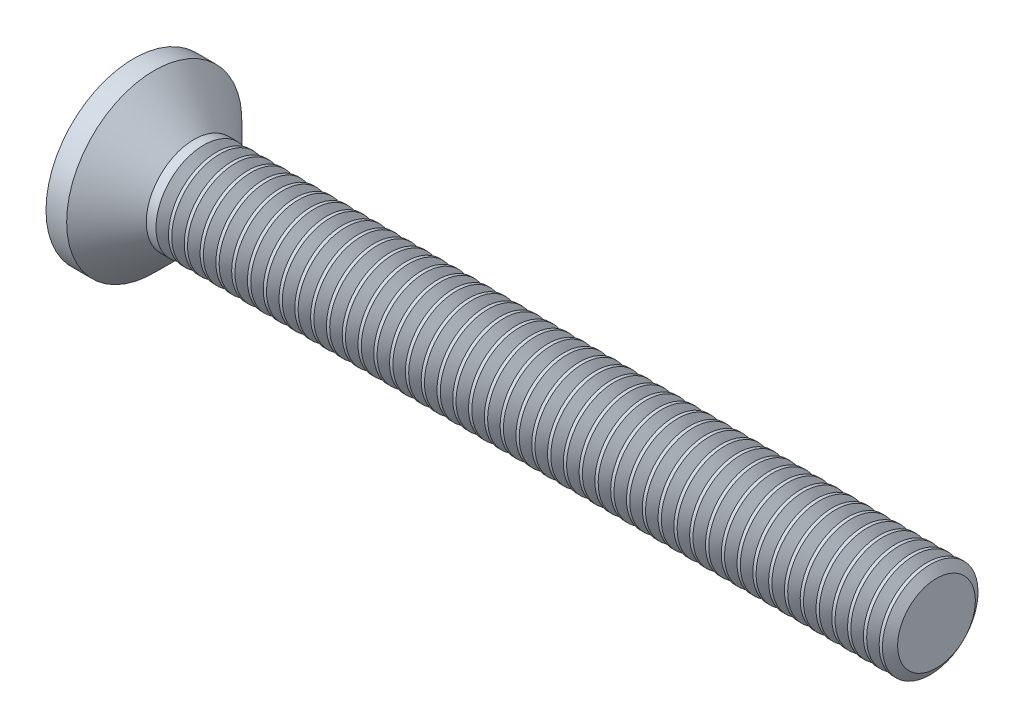
SolidWorks part; units mm, degrees
revolve "Base-Revolve" add sketch "BodySke" angle 360 about L4
sketch "BodySke" plane through (0, 0, 0) normal (0, 0, 1) x (1, 0, 0)
  line L0 (0, 0) -> (25.7277, 0)
  line L1 (25.7277, 0) -> (25.7277, 1.5)
  line L2 (25.7277, 1.5) -> (2.4277, 1.5)
  line L3 (2.4277, 1.5) -> (-7.1953, 11.123) construction
  line L4 (-15.875, 0) -> (82.55, 0) construction
  line L5 (2.4277, -1.5) -> (-7.1953, -11.123) construction
  line L6 (2.9277, 4.675) -> (2.9277, -11.2) construction
  line L7 (0.7277, 8.7375) -> (0.7277, -7.1375) construction
  line L8 (2.4277, 1.5) -> (1.1777, 2.75)
  line L9 (1.1777, 2.75) -> (0.53, 2.75)
  arc A0 (0, 0) -> (0.53, 2.75) centre (7.4, 0) cw
  arc A1 (0.7277, 3.2) -> (0, 0) centre (7.4, 0) ccw construction
  dimension "Crown_rad" = 7.4
  dimension "Diameter" = 3
  dimension "Advance" = 0.5
  dimension "Thread_nom" = 25
  dimension "Head_ang" = 90
  dimension "D3" = 6.4
  dimension "Side_ht" = 1.7
  dimension "D4" = 0.7277
  dimension "Length" = 25
  dimension "Head_dia" = 5.5
cosmetic thread "ThreadCosmetic" [suppressed] parameters "Thread_length"=22.8, "Thread_minor"=2.439
ref_plane "Plane1" through (0, 0, 0) normal (0, 0, 1) x (1, 0, 0)
ref_plane "Plane2" through (0, 0, 0) normal (0, 1, 0) x (1, 0, 0)
ref_plane "Plane3" through (0, 0, 0) normal (1, 0, 0) x (0, 0, -1)
sketch "Sketch2" plane through (0, 0, 0) normal (1, 0, 0) x (0, 0, -1)
  line L0 (2.75, -0.5) -> (-2.75, -0.5)
  line L1 (2.75, -0.5) -> (2.75, 0.5)
  line L2 (-2.75, 0.5) -> (2.75, 0.5)
  line L3 (-2.75, 0.5) -> (-2.75, -0.5)
  dimension "D1" = 5.5
  dimension "Slot_width" = 1
  dimension "D3" = 2.75
  dimension "D4" = 0.5
extrude "Slot" [suppressed] cut sketch "Sketch2" along normal blind 1.5
sketch "Sketch3" plane through (0, 0, 0) normal (1, 0, 0) x (0, 0, -1)
  line L0 (0.415, -1.72) -> (-0.415, -1.72)
  line L1 (0.415, -1.72) -> (0.415, 1.72)
  line L2 (-0.415, 1.72) -> (0.415, 1.72)
  line L3 (-0.415, 1.72) -> (-0.415, -1.72)
  dimension "Cross_width" = 0.83
  dimension "D1" = 0.415
  dimension "Cross_dia" = 3.44
  dimension "D2" = 1.72
ref_plane "Plane4" through (2.33, 0, 0) normal (1, 0, 0) x (0, 0, -1)
sketch "Sketch4" plane through (2.33, 0, 0) normal (1, 0, 0) x (0, 0, -1)
  line L0 (0.2075, -0.2075) -> (-0.2075, -0.2075)
  line L1 (0.2075, -0.2075) -> (0.2075, 0.2075)
  line L2 (-0.2075, 0.2075) -> (0.2075, 0.2075)
  line L3 (-0.2075, 0.2075) -> (-0.2075, -0.2075)
  dimension "D1" = 0.415
  dimension "D2" = 0.415
  dimension "D3" = 0.2075
  dimension "D4" = 0.2075
loft "Cross" cut profiles "Sketch3", "Sketch4"
pattern_circular "CirPattern1" count 2 every 90 about axis through (0, 0, 0) along (1, 0, 0) of "Cross"
sketch "ThdSchSke" plane through (0, 0, 0) normal (0, 0, 1) x (1, 0, 0)
  line L0 (2.9277, -1.2195) -> (2.7313, -1.5)
  line L1 (2.9277, -1.2195) -> (3.1241, -1.5)
  line L2 (3.1241, -1.5) -> (3.1241, -1.875)
  line L3 (-3.175, 0) -> (5.1513, 0) construction
  line L5 (3.1241, -1.875) -> (2.7313, -1.875)
  line L6 (2.7313, -1.875) -> (2.7313, -1.5)
  line L8 (25.7277, -1.5) -> (25.7277, 1.5) construction
  dimension "Diameter" = 3
  dimension "Thread_minor" = 2.439
  dimension "Start" = 22.8
revolve "ThreadSchematic" cut sketch "ThdSchSke" angle 360 about L3
pattern_linear "ThdSchPat" count 47 spacing 0.4957 along (1, 0, 0) of "ThreadSchematic"
equation "\"D1@Sketch2\" = \"Head_dia@BodySke\""
equation "\"D3@Sketch2\" = \"D1@Sketch2\" / 2"
equation "\"D4@Sketch2\" = \"Slot_width@Sketch2\" / 2"
equation "\"D1@Sketch3\" = \"Cross_width@Sketch3\" / 2"
equation "\"D2@Sketch3\" = \"Cross_dia@Sketch3\" / 2"
equation "\"D1@Sketch4\" = \"Cross_width@Sketch3\"*.5"
equation "\"D2@Sketch4\" = \"D1@Sketch4\""
equation "\"D3@Sketch4\" = \"D1@Sketch4\" / 2"
equation "\"D4@Sketch4\" = \"D2@Sketch4\" / 2"
equation "\"Thread_length@ThreadCosmetic\" = ((sgn( (\"Length@BodySke\" - \"Advance@BodySke\" - \"Side_ht@BodySke\" ) - \"Thread_nom@BodySke\" )-1)*( (\"Length@BodySke\" - \"Advance@BodySke\" - \"Side_ht@BodySke\" ) - \"Thread_nom@BodySke\" ))/-2+ \"Thread_nom@BodySke\""
equation "\"Thread_minor@ThdSchSke\" = \"Thread_minor@ThreadCosmetic\""
equation "\"Diameter@ThdSchSke\" = \"Diameter@BodySke\""
equation "\"Overcut@ThdSchSke\" = \"Diameter@BodySke\" * 1.25"
equation "\"Start@ThdSchSke\" =  \"Thread_length@ThreadCosmetic\""
equation "\"Num_threads@ThdSchPat\" = int( \"Thread_length@ThreadCosmetic\" / \"Advance@BodySke\" + 0.999 )  + 1"
equation "\"Advance@ThdSchPat\" = \"Thread_length@ThreadCosmetic\" /  (\"Num_threads@ThdSchPat\" - 1) 'relax it"
